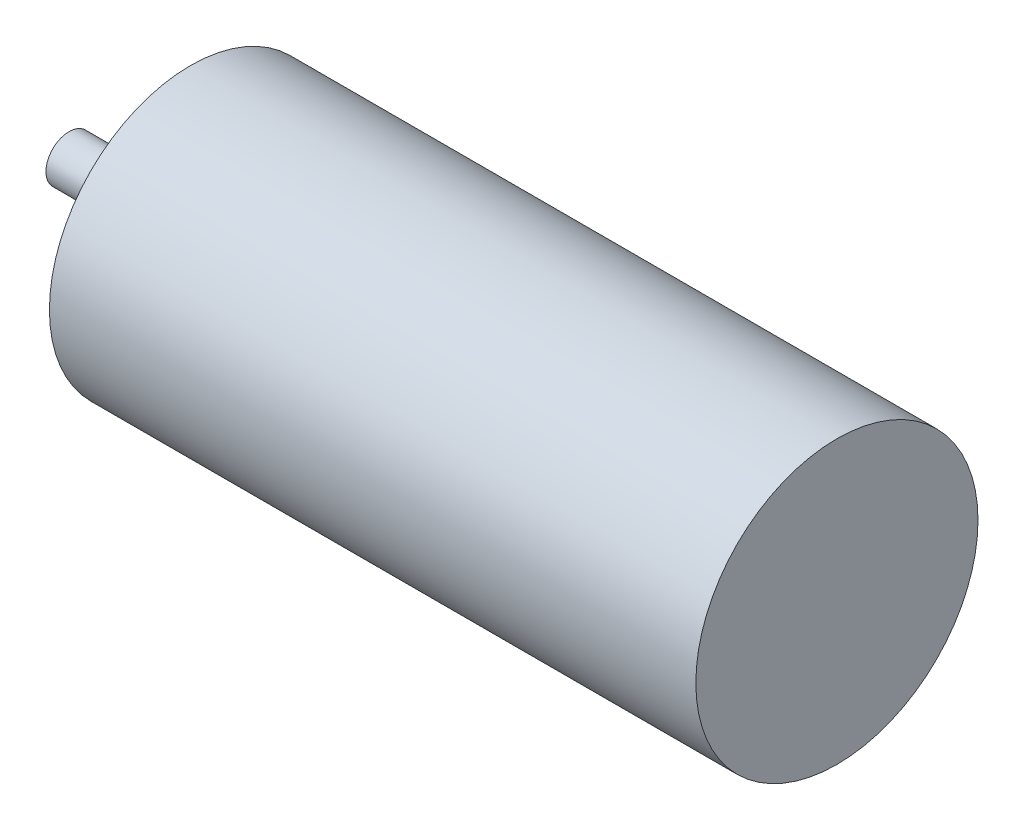
SolidWorks part; units mm, degrees
ref_plane "Přední rovina" through (0, 0, 0) normal (0, 0, 1) x (1, 0, 0)
ref_plane "Horní rovina" through (0, 0, 0) normal (0, 1, 0) x (1, 0, 0)
ref_plane "Pravá rovina" through (0, 0, 0) normal (1, 0, 0) x (0, 0, -1)
sketch "Skica2" plane through (0, 0, 0) normal (0, 0, 1) x (1, 0, 0)
  line L1 (0, 0) -> (-55.9, 0)
  line L2 (0, 0) -> (0, 12.2)
  line L3 (0, 12.2) -> (-55.9, 12.2)
  line L4 (-55.9, 0) -> (-55.9, 12.2)
  line L5 (-55.9, 0) -> (-57.9, 0)
  line L6 (-55.9, 0) -> (-55.9, 3.5)
  line L7 (-55.9, 3.5) -> (-57.9, 3.5)
  line L8 (-57.9, 0) -> (-57.9, 3.5)
  line L9 (-57.9, 0) -> (-66.4, 0)
  line L10 (-57.9, 0) -> (-57.9, 2)
  line L11 (-57.9, 2) -> (-66.4, 2)
  line L12 (-66.4, 0) -> (-66.4, 2)
  dimension "D1" = 55.9
  dimension "D2" = 12.2
  dimension "D3" = 3.5
  dimension "D4" = 2
  dimension "D5" = 8.5
  dimension "D6" = 2
revolve "Rotovat1" add sketch "Skica2" angle 360 about L1
